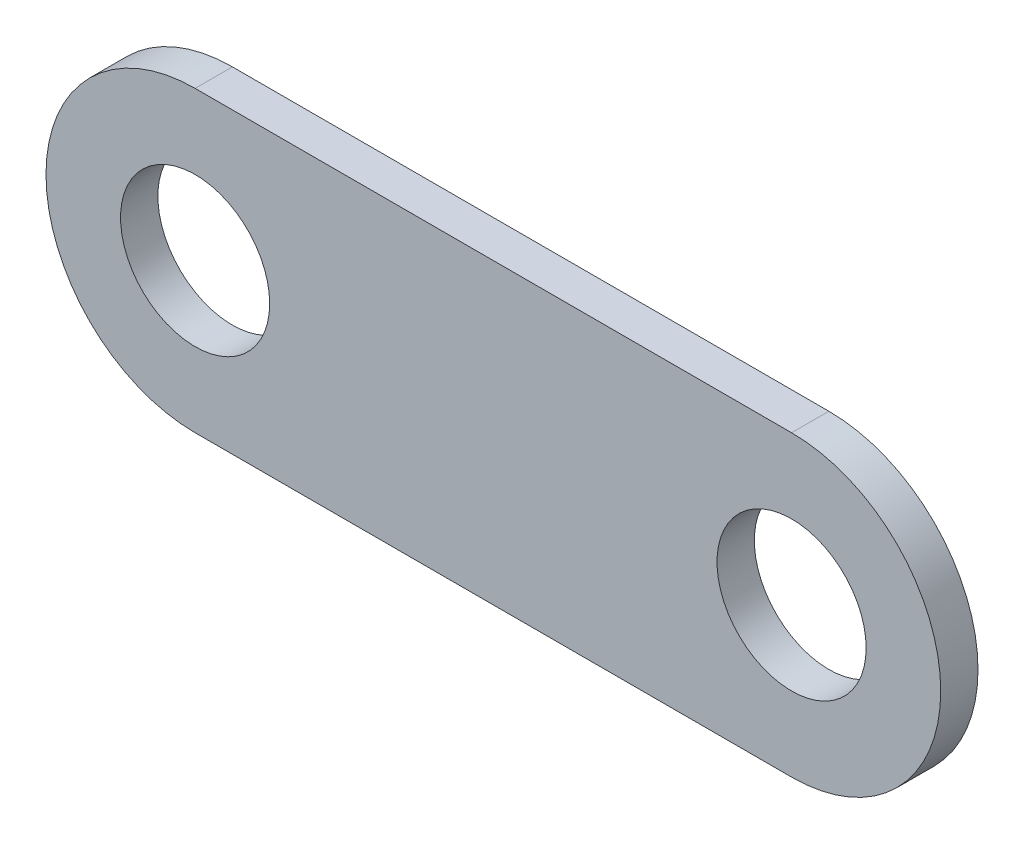
SolidWorks part; units mm, degrees
material "Pure Lead"
ref_plane "Front Plane" through (0, 0, 0) normal (0, 0, 1) x (1, 0, 0)
ref_plane "Top Plane" through (0, 0, 0) normal (0, 1, 0) x (1, 0, 0)
ref_plane "Right Plane" through (0, 0, 0) normal (1, 0, 0) x (0, 0, -1)
sketch "Sketch1" plane through (0, 0, 0) normal (0, 0, 1) x (1, 0, 0)
  line L0 (51.5131, 21.5571) -> (-28.4869, 21.5571)
  line L1 (-28.4869, -18.4429) -> (51.5131, -18.4429)
  arc A0 (51.5131, -18.4429) -> (51.5131, 21.5571) centre (51.5131, 1.5571) ccw
  arc A1 (-28.4869, 21.5571) -> (-28.4869, -18.4429) centre (-28.4869, 1.5571) ccw
  dimension "D2" = 20
  dimension "D1" = 80
extrude "Extrude1" add sketch "Sketch1" along normal blind 5
sketch "Sketch2" plane through (0, 0, 5) normal (0, 0, 1) x (1, 0, 0)
  circle A0 centre (-28.4869, 1.5571) radius 10
  circle A1 centre (51.5131, 1.5571) radius 10
  dimension "D1" = 20
extrude "Cut-Extrude1" cut sketch "Sketch2" against normal through all
